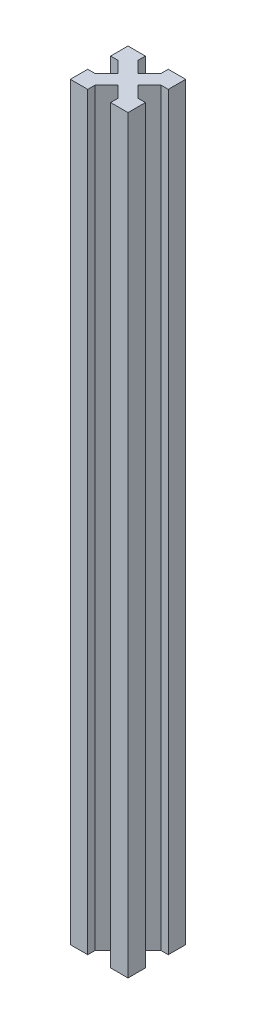
SolidWorks part; units mm, degrees
ref_plane "Plan de face" through (0, 0, 0) normal (0, 0, 1) x (1, 0, 0)
ref_plane "Plan de dessus" through (0, 0, 0) normal (0, 1, 0) x (1, 0, 0)
ref_plane "Plan de droite" through (0, 0, 0) normal (1, 0, 0) x (0, 0, -1)
sketch "Esquisse1" plane through (0, 0, 0) normal (0, 1, 0) x (1, 0, 0)
  line L0 (-2.5, 17.5) -> (-17.5, 17.5)
  line L1 (0, 0) -> (-20, 0)
  line L2 (0, 0) -> (0, 20)
  line L3 (0, 20) -> (-20, 20)
  line L4 (-20, 0) -> (-20, 20)
  line L5 (0, 20) -> (-20, 0) construction
  line L6 (-17.5, 2.5) -> (-17.5, 17.5)
  line L11 (-2.5, 2.5) -> (-17.5, 2.5)
  line L12 (-2.5, 2.5) -> (-2.5, 17.5)
  line L13 (-20, 20) -> (0, 0) construction
  line L14 (-26.9957, 23.4601) -> (-23.4601, 26.9957)
  line L15 (-26.9957, 23.4601) -> (3.4601, -6.9957)
  line L16 (-23.4601, 26.9957) -> (6.9957, -3.4601)
  line L17 (3.4601, -6.9957) -> (6.9957, -3.4601)
  line L18 (-26.9957, 23.4601) -> (6.9957, -3.4601) construction
  line L19 (-23.4601, 26.9957) -> (3.4601, -6.9957) construction
  line L20 (-10, 20) -> (-10, 0) construction
  line L21 (-23.4601, -6.9957) -> (-26.9957, -3.4601)
  line L22 (3.4601, 26.9957) -> (-26.9957, -3.4601)
  line L23 (6.9957, 23.4601) -> (-23.4601, -6.9957)
  line L24 (6.9957, 23.4601) -> (3.4601, 26.9957)
  line L25 (-17.5, 13.9645) -> (-20, 13.9645)
  line L26 (-20, 10) -> (0, 10) construction
  line L27 (-17.5, 6.0355) -> (-20, 6.0355)
  line L28 (-2.5, 6.0355) -> (0, 6.0355)
  line L29 (-2.5, 13.9645) -> (0, 13.9645)
  line L30 (-2.5, 6.0355) -> (0, 6.0355)
  line L31 (-2.5, 13.9645) -> (0, 13.9645)
  line L32 (-13.9645, 2.5) -> (-13.9645, 0)
  line L33 (-6.0355, 17.5) -> (-6.0355, 20)
  line L34 (-13.9645, 17.5) -> (-13.9645, 20)
  line L35 (-6.0355, 2.5) -> (-6.0355, 0)
  point P11 (-10, 10)
  dimension "D1" = 20
  dimension "D2" = 20
  dimension "D3" = 7.3934
  dimension "D4" = 2.5
  dimension "D5" = 43.071
  dimension "D6" = 2.5
extrude "Boss.-Extru.1" add sketch "Esquisse1" along normal blind 260 contours L15 L35 L1 | L16 L12 L11 L15 L1 L2 | L28 L16 L2 | L16 L23 L15 L11 L12 | L32 L23 L1 | L23 L11 L6 L22 L4 L1 | L22 L27 L4 | L23 L15 L22 L6 L11 | L23 L16 L22 L15 | L23 L12 L0 L22 L16 | L23 L2 L3 L22 L0 L12 | L23 L29 L2 | L33 L22 L3 | L16 L34 L3 | L16 L3 L4 L15 L6 L0 | L25 L15 L4 | L22 L16 L0 L6 L15
